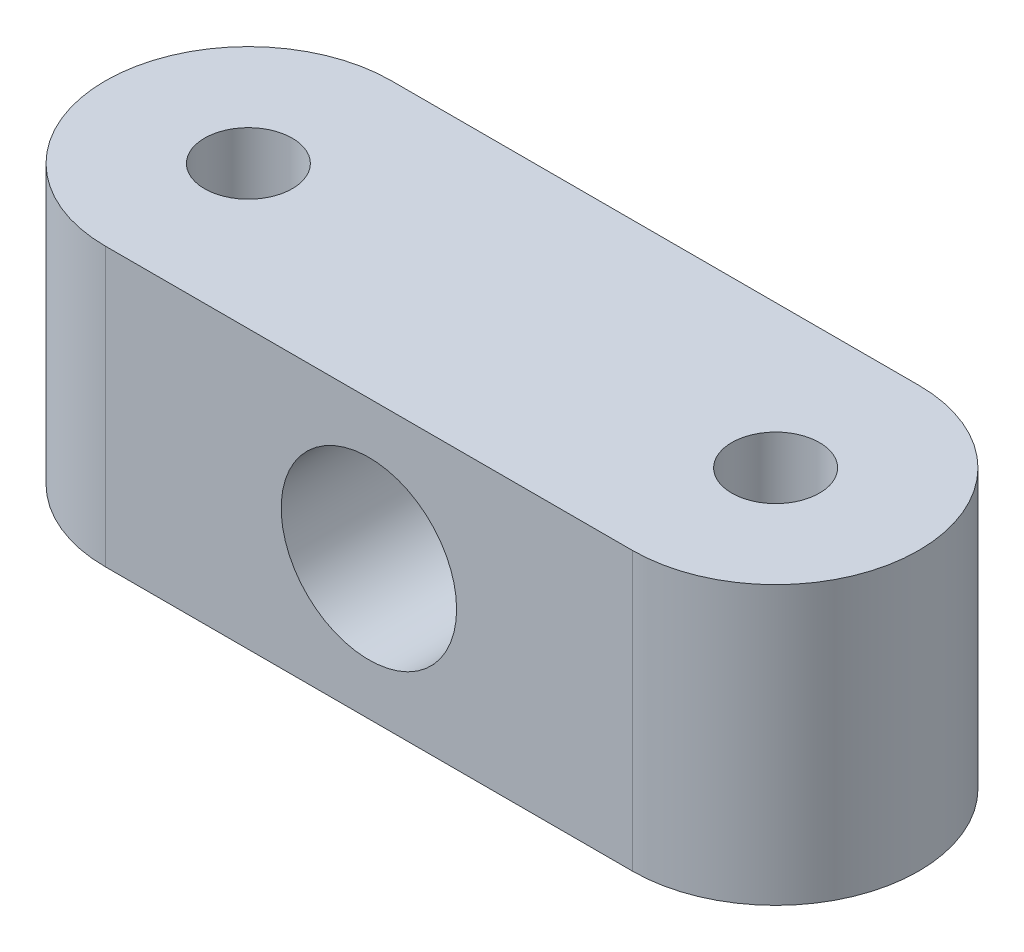
SolidWorks part; units mm, degrees
ref_plane "Front Plane" through (0, 0, 0) normal (0, 0, 1) x (1, 0, 0)
ref_plane "Top Plane" through (0, 0, 0) normal (0, 1, 0) x (1, 0, 0)
ref_plane "Right Plane" through (0, 0, 0) normal (1, 0, 0) x (0, 0, -1)
sketch "Sketch1" plane through (0, 0, 0) normal (0, 1, 0) x (1, 0, 0)
  line L0 (0, 0) -> (72.1289, 0) construction
  line L1 (0, 19.5778) -> (72.1289, 19.5778)
  line L2 (0, -19.5778) -> (72.1289, -19.5778)
  arc A0 (0, 19.5778) -> (0, -19.5778) centre (0, 0) ccw
  arc A1 (72.1289, -19.5778) -> (72.1289, 19.5778) centre (72.1289, 0) ccw
  circle A2 centre (0, 0) radius 6
  circle A3 centre (72.1289, 0) radius 6
  point P3 (36.0644, 0)
  dimension "D1" = 12
extrude "Boss-Extrude1" add sketch "Sketch1" along normal blind 38 contours A3 | A2 | L1 A1 L2 A0
sketch "Sketch3" plane through (0, 0, 19.5778) normal (0, 0, 1) x (1, 0, 0)
  line L0 (36.0644, 0) -> (36.0644, 38) construction
  line L1 (0, 0) -> (72.1289, 0) construction
  line L2 (0, 38) -> (72.1289, 38) construction
  circle A0 centre (36.0644, 19) radius 12
  dimension "D1" = 24
extrude "Cut-Extrude2" cut sketch "Sketch3" against normal blind 98 contours A0
cosmetic thread "Cosmetic Thread1" parameters "D1"=5, "D2"=27
